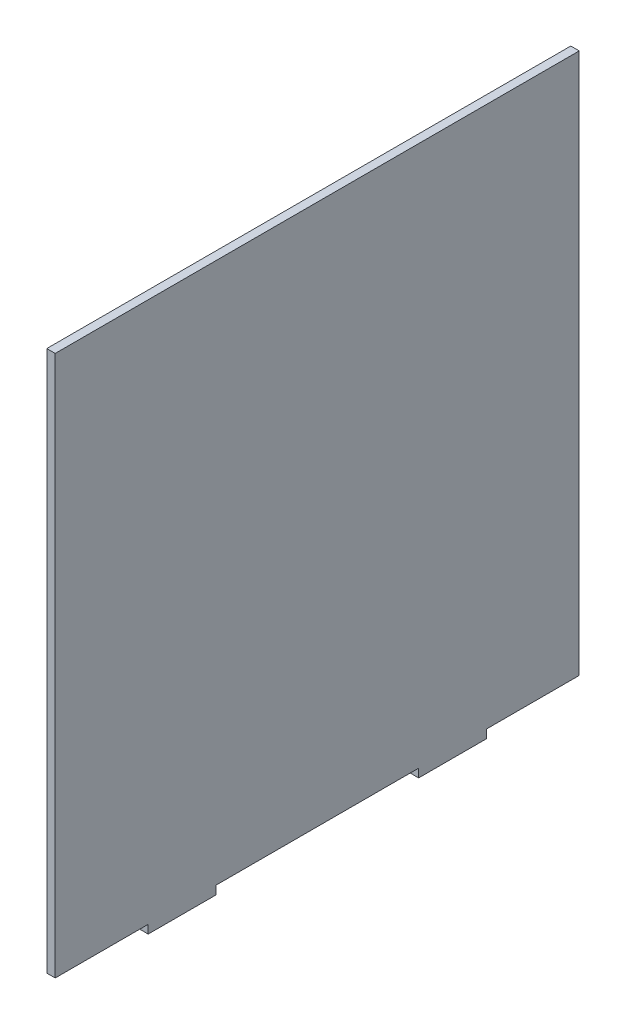
SolidWorks part; units mm, degrees
ref_plane "Front Plane" through (0, 0, 0) normal (0, 0, 1) x (1, 0, 0)
ref_plane "Top Plane" through (0, 0, 0) normal (0, 1, 0) x (1, 0, 0)
ref_plane "Right Plane" through (0, 0, 0) normal (1, 0, 0) x (0, 0, -1)
sketch "Sketch1" plane through (0, 0, 0) normal (1, 0, 0) x (0, 0, -1)
  line L1 (0, 0) -> (196.85, 0)
  line L2 (0, 0) -> (0, 203.2)
  line L3 (0, 203.2) -> (196.85, 203.2)
  line L4 (196.85, 0) -> (196.85, 203.2)
  dimension "D1" = 203.2
  dimension "D2" = 196.85
extrude "Boss-Extrude1" add sketch "Sketch1" along normal blind 3.175
sketch "Sketch2" [suppressed] plane through (3.175, 0, 0) normal (1, 0, 0) x (0, 0, -1)
  line L0 (87.63, 88.9) -> (109.22, 88.9) construction
  line L1 (196.85, 203.2) -> (0, 203.2) construction
  line L2 (0, 0) -> (196.85, 0) construction
  circle A0 centre (87.63, 88.9) radius 8.89
  circle A1 centre (109.22, 88.9) radius 8.89
  point P6 (98.425, 203.2)
  point P7 (98.425, 88.9)
  dimension "D1" = 17.78
  dimension "D2" = 21.59
  dimension "D3" = 88.9
extrude "Cut-Extrude1" [suppressed] cut sketch "Sketch2" against normal through all
sketch "Sketch3" plane through (0, 0, 0) normal (0, -1, 0) x (1, 0, 0)
  line L0 (0, 0) -> (0, -196.85) construction
  line L1 (0, -34.925) -> (3.175, -34.925)
  line L2 (0, -34.925) -> (0, -60.325)
  line L3 (0, -60.325) -> (3.175, -60.325)
  line L4 (3.175, -34.925) -> (3.175, -60.325)
  line L5 (3.175, 0) -> (3.175, -196.85) construction
  line L6 (3.175, 0) -> (0, 0) construction
  line L7 (0, -136.525) -> (3.175, -136.525)
  line L8 (0, -136.525) -> (0, -161.925)
  line L9 (0, -161.925) -> (3.175, -161.925)
  line L10 (3.175, -136.525) -> (3.175, -161.925)
  line L11 (3.175, -196.85) -> (0, -196.85) construction
  dimension "D1" = 25.4
  dimension "D2" = 25.4
  dimension "D3" = 34.925
  dimension "D4" = 34.925
extrude "Boss-Extrude2" add sketch "Sketch3" along normal blind 3.175
